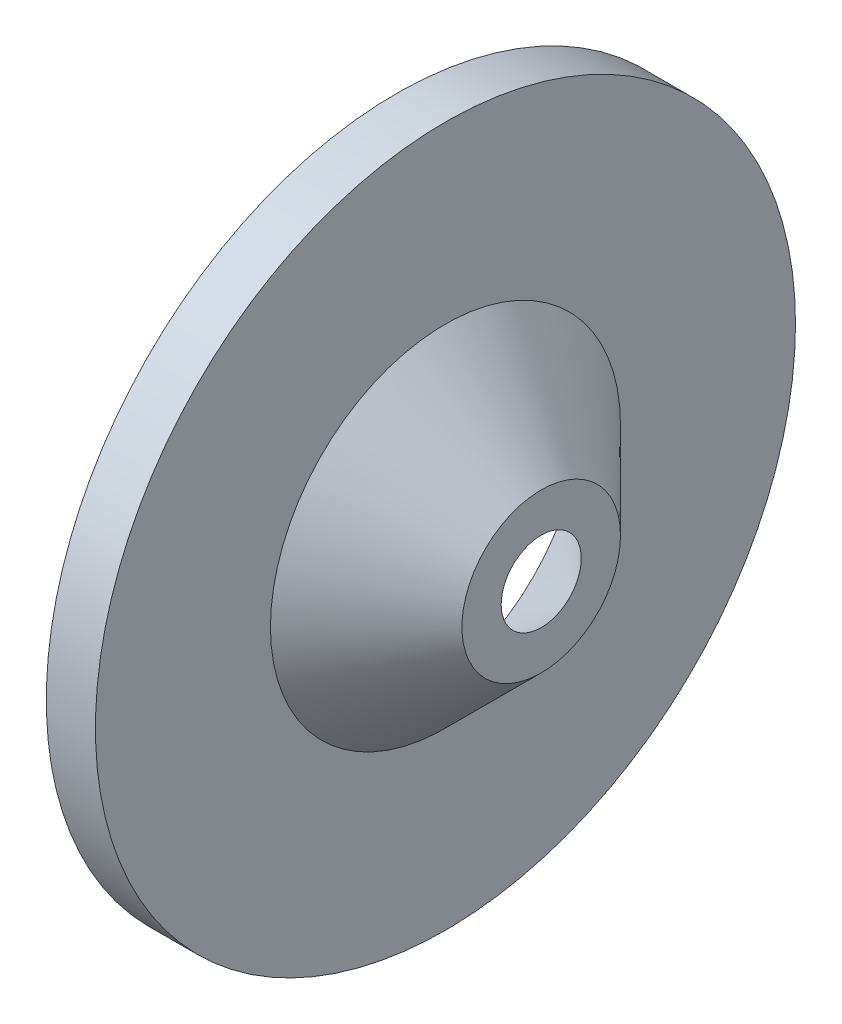
SolidWorks part; units mm, degrees
ref_plane "Alzado" through (0, 0, 0) normal (0, 0, 1) x (1, 0, 0)
ref_plane "Planta" through (0, 0, 0) normal (0, 1, 0) x (1, 0, 0)
ref_plane "Vista lateral" through (0, 0, 0) normal (1, 0, 0) x (0, 0, -1)
sketch "Croquis1" plane through (0, 0, 0) normal (0, 0, 1) x (1, 0, 0)
  line L0 (0, 53.4279) -> (0, -72.7104)
  line L1 (0, -72.7104) -> (17.7032, -72.7104)
  line L2 (17.7032, -72.7104) -> (17.7032, -9.6413)
  line L3 (17.7032, -9.6413) -> (52.2035, 24.859)
  line L4 (52.2035, 24.859) -> (52.2035, 53.4279)
  line L5 (52.2035, 53.4279) -> (0, 53.4279)
revolve "Revolución1" add sketch "Croquis1" angle 360 about L5
shell "Vaciado1" thickness 10
